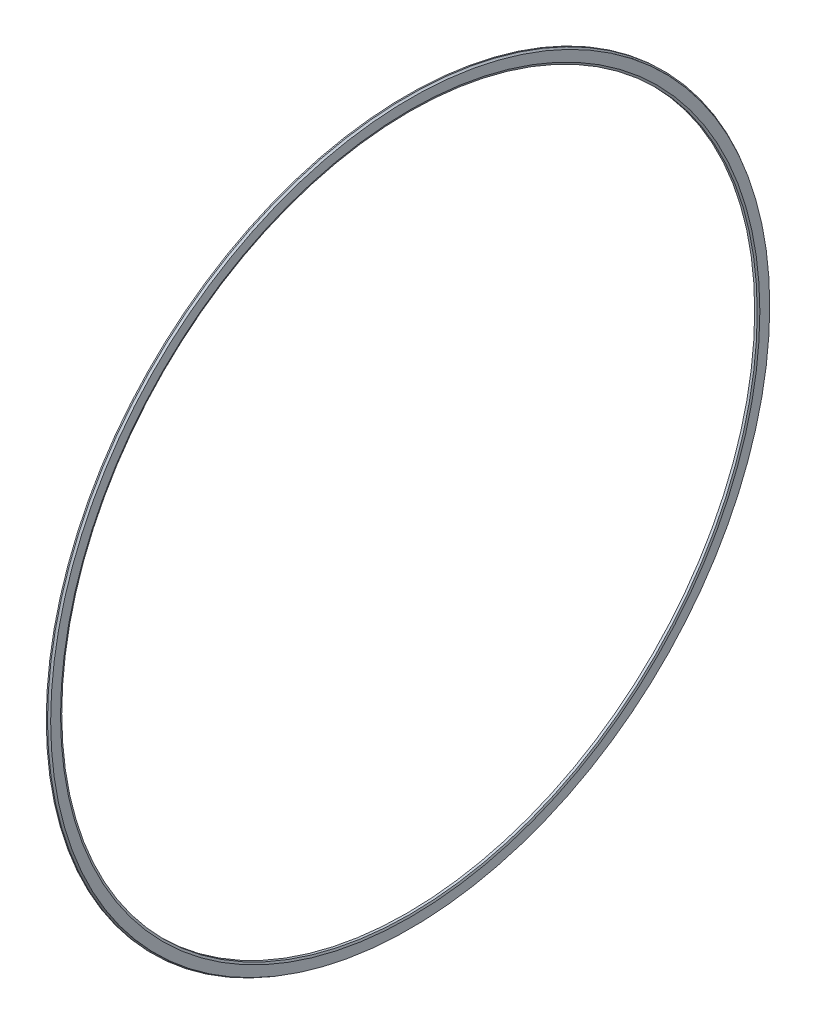
SolidWorks part; units mm, degrees
ref_plane "前视基准面" through (0, 0, 0) normal (0, 0, 1) x (1, 0, 0)
ref_plane "上视基准面" through (0, 0, 0) normal (0, 1, 0) x (1, 0, 0)
ref_plane "右视基准面" through (0, 0, 0) normal (1, 0, 0) x (0, 0, -1)
sketch "草图1" plane through (0, 0, 0) normal (0, 0, 1) x (1, 0, 0)
  line L0 (0, 0) -> (0, 44.55) construction
  line L1 (0, 44.55) -> (0.15, 44.55)
  line L2 (0.4, 44.408) -> (0.4, 43.186)
  line L3 (0.4, 43.186) -> (0.3121, 42.95)
  line L4 (0.3121, 42.95) -> (0, 42.95)
  line L5 (0, 42.95) -> (0, 44.55)
  line L6 (0, 0) -> (2.6472, 0) construction
  arc A0 (0.15, 44.55) -> (0.4, 44.408) centre (0.4406, 44.7706) ccw
  dimension "D4" = 0.3648
  dimension "D1" = 0.4
  dimension "D2" = 1.6
  dimension "D3" = 0.15
  dimension "D5" = 44.55
  dimension "D6" = 0.236
revolve "旋转1" add sketch "草图1" angle 360 about L6
